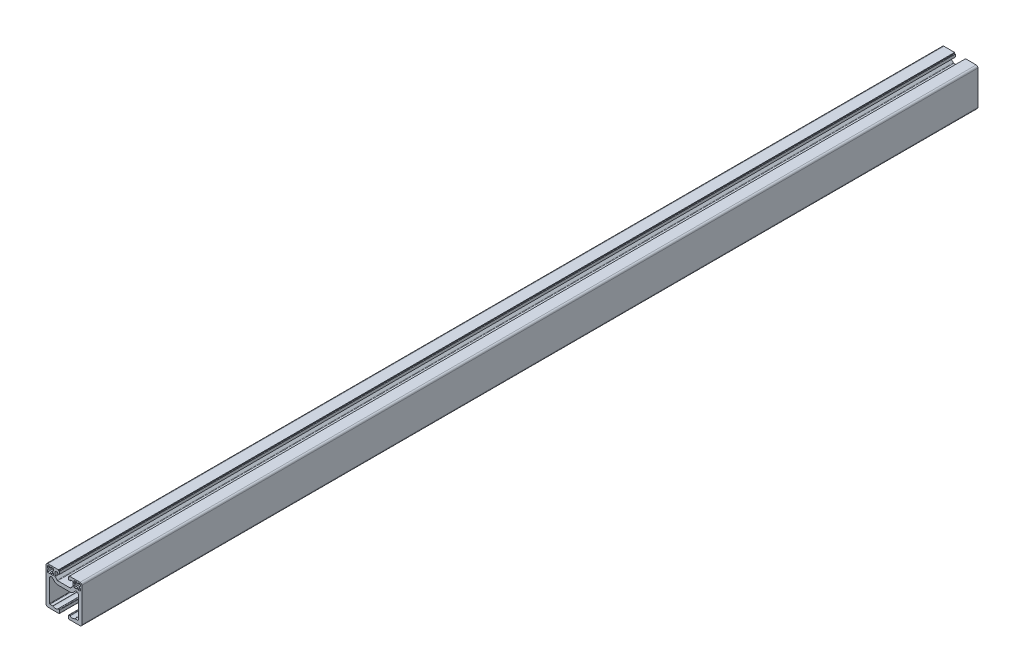
SolidWorks part; units mm, degrees
material "АД31 ГОСТ 4784-97"
ref_plane "Спереди" through (0, 0, 0) normal (0, 0, 1) x (1, 0, 0)
ref_plane "Сверху" through (0, 0, 0) normal (0, 1, 0) x (1, 0, 0)
ref_plane "Справа" through (0, 0, 0) normal (1, 0, 0) x (0, 0, -1)
sketch "Эскиз1" plane through (0, 0, 0) normal (0, 0, 1) x (1, 0, 0)
  line L0 (-15.5, -17) -> (-12.5, -17)
  line L1 (-6.5, -17) -> (-5.5, -17)
  line L2 (-5, -17.5) -> (-5, -20.5)
  line L3 (-5.5, -21) -> (-18, -21)
  line L4 (-20, -19) -> (-20, 19)
  line L5 (-18, 21) -> (-6.1, 21)
  line L6 (-6.1, 21) -> (-6.1, 20)
  line L7 (-6.1, 20) -> (-5.1, 20)
  line L8 (-5.1, 20) -> (-5.1, 17)
  line L9 (-5.1, 17) -> (-7.1, 17)
  line L10 (-7.1, 17) -> (-7.1, 18)
  line L11 (-7.1, 18) -> (-9, 18)
  line L12 (-10, 17) -> (-10, 13.182)
  line L13 (-9.7071, 12.4749) -> (-7.5251, 10.2929)
  line L14 (-6.818, 10) -> (6.818, 10)
  line L15 (7.5251, 10.2929) -> (9.7071, 12.4749)
  line L16 (10, 13.182) -> (10, 17)
  line L17 (9, 18) -> (7.1, 18)
  line L18 (7.1, 18) -> (7.1, 17)
  line L19 (7.1, 17) -> (5.1, 17)
  line L20 (5.1, 17) -> (5.1, 20)
  line L21 (5.1, 20) -> (6.1, 20)
  line L22 (6.1, 20) -> (6.1, 21)
  line L23 (6.1, 21) -> (18, 21)
  line L24 (20, 19) -> (20, -19)
  line L25 (18, -21) -> (5.5, -21)
  line L26 (5, -20.5) -> (5, -17.5)
  line L27 (5.5, -17) -> (6.5, -17)
  line L28 (12.5, -17) -> (15.5, -17)
  line L29 (16, -16.5) -> (16, 8.2825)
  line L30 (12.5858, 9.6967) -> (10.3536, 7.4645)
  line L31 (6.818, 6) -> (-6.818, 6)
  line L32 (-10.3536, 7.4645) -> (-12.5858, 9.6967)
  line L33 (-16, 8.2825) -> (-16, -16.5)
  line L34 (-11.5, 12.5) -> (-14.2, 12.5)
  line L35 (17.5, 16.8) -> (18.5, 16.8)
  line L36 (18.5, 16.8) -> (18.5, 18.5)
  line L37 (17.5, 15.2) -> (17.5, 16.8)
  line L38 (18.5, 15.2) -> (17.5, 15.2)
  line L39 (17.5, 19.5) -> (15.8, 19.5)
  line L40 (18.5, 12.5) -> (18.5, 15.2)
  line L41 (15.8, 19.5) -> (15.8, 18.5)
  line L42 (15.8, 12.5) -> (18.5, 12.5)
  line L43 (15.8, 18.5) -> (14.2, 18.5)
  line L44 (15.8, 13.5) -> (15.8, 12.5)
  line L45 (14.2, 18.5) -> (14.2, 19.5)
  line L46 (14.2, 13.5) -> (15.8, 13.5)
  line L47 (14.2, 19.5) -> (11.5, 19.5)
  line L48 (14.2, 12.5) -> (14.2, 13.5)
  line L49 (11.5, 19.5) -> (11.5, 16.8)
  line L50 (11.5, 12.5) -> (14.2, 12.5)
  line L51 (11.5, 16.8) -> (12.5, 16.8)
  line L52 (11.5, 15.2) -> (11.5, 12.5)
  line L53 (12.5, 16.8) -> (12.5, 15.2)
  line L54 (12.5, 15.2) -> (11.5, 15.2)
  line L55 (-12.5, 16.8) -> (-11.5, 16.8)
  line L56 (-11.5, 16.8) -> (-11.5, 19.5)
  line L57 (-12.5, 15.2) -> (-12.5, 16.8)
  line L58 (-11.5, 19.5) -> (-14.2, 19.5)
  line L59 (-11.5, 15.2) -> (-12.5, 15.2)
  line L60 (-14.2, 19.5) -> (-14.2, 18.5)
  line L61 (-11.5, 12.5) -> (-11.5, 15.2)
  line L62 (-14.2, 18.5) -> (-15.8, 18.5)
  line L64 (-15.8, 18.5) -> (-15.8, 19.5)
  line L65 (-14.2, 13.5) -> (-14.2, 12.5)
  line L66 (-15.8, 19.5) -> (-17.5, 19.5)
  line L67 (-15.8, 13.5) -> (-14.2, 13.5)
  line L68 (-15.8, 12.5) -> (-15.8, 13.5)
  line L69 (-18.5, 18.5) -> (-18.5, 16.8)
  line L70 (-18.5, 12.5) -> (-15.8, 12.5)
  line L71 (-18.5, 16.8) -> (-17.5, 16.8)
  line L72 (-18.5, 15.2) -> (-18.5, 12.5)
  line L73 (-17.5, 16.8) -> (-17.5, 15.2)
  line L74 (-17.5, 15.2) -> (-18.5, 15.2)
  arc A0 (-12.2, -17.1) -> (-12.5, -17) centre (-12.5, -17.5) ccw
  arc A1 (-12.2, -17.1) -> (-6.8, -17.1) centre (-9.5, -13.5) ccw
  arc A2 (-6.5, -17) -> (-6.8, -17.1) centre (-6.5, -17.5) ccw
  arc A3 (-5, -17.5) -> (-5.5, -17) centre (-5.5, -17.5) ccw
  arc A4 (-5.5, -21) -> (-5, -20.5) centre (-5.5, -20.5) ccw
  arc A5 (-20, -19) -> (-18, -21) centre (-18, -19) ccw
  arc A6 (-18, 21) -> (-20, 19) centre (-18, 19) ccw
  arc A7 (-9, 18) -> (-10, 17) centre (-9, 17) ccw
  arc A8 (-10, 13.182) -> (-9.7071, 12.4749) centre (-9, 13.182) ccw
  arc A9 (-7.5251, 10.2929) -> (-6.818, 10) centre (-6.818, 11) ccw
  arc A10 (6.818, 10) -> (7.5251, 10.2929) centre (6.818, 11) ccw
  arc A11 (9.7071, 12.4749) -> (10, 13.182) centre (9, 13.182) ccw
  arc A12 (10, 17) -> (9, 18) centre (9, 17) ccw
  arc A13 (20, 19) -> (18, 21) centre (18, 19) ccw
  arc A14 (18, -21) -> (20, -19) centre (18, -19) ccw
  arc A15 (5, -20.5) -> (5.5, -21) centre (5.5, -20.5) ccw
  arc A16 (5.5, -17) -> (5, -17.5) centre (5.5, -17.5) ccw
  arc A17 (6.8, -17.1) -> (6.5, -17) centre (6.5, -17.5) ccw
  arc A18 (6.8, -17.1) -> (12.2, -17.1) centre (9.5, -13.5) ccw
  arc A19 (12.5, -17) -> (12.2, -17.1) centre (12.5, -17.5) ccw
  arc A20 (15.5, -17) -> (16, -16.5) centre (15.5, -16.5) ccw
  arc A21 (16, 8.2825) -> (12.5858, 9.6967) centre (14, 8.2825) ccw
  arc A22 (6.818, 6) -> (10.3536, 7.4645) centre (6.818, 11) ccw
  arc A23 (-10.3536, 7.4645) -> (-6.818, 6) centre (-6.818, 11) ccw
  arc A24 (-12.5858, 9.6967) -> (-16, 8.2825) centre (-14, 8.2825) ccw
  arc A25 (-16, -16.5) -> (-15.5, -17) centre (-15.5, -16.5) ccw
  arc A26 (18.5, 18.5) -> (17.5, 19.5) centre (17.5, 18.5) ccw
  arc A27 (-17.5, 19.5) -> (-18.5, 18.5) centre (-17.5, 18.5) ccw
extrude "Бобышка-Вытянуть1" add sketch "Эскиз1" along normal blind 1000
